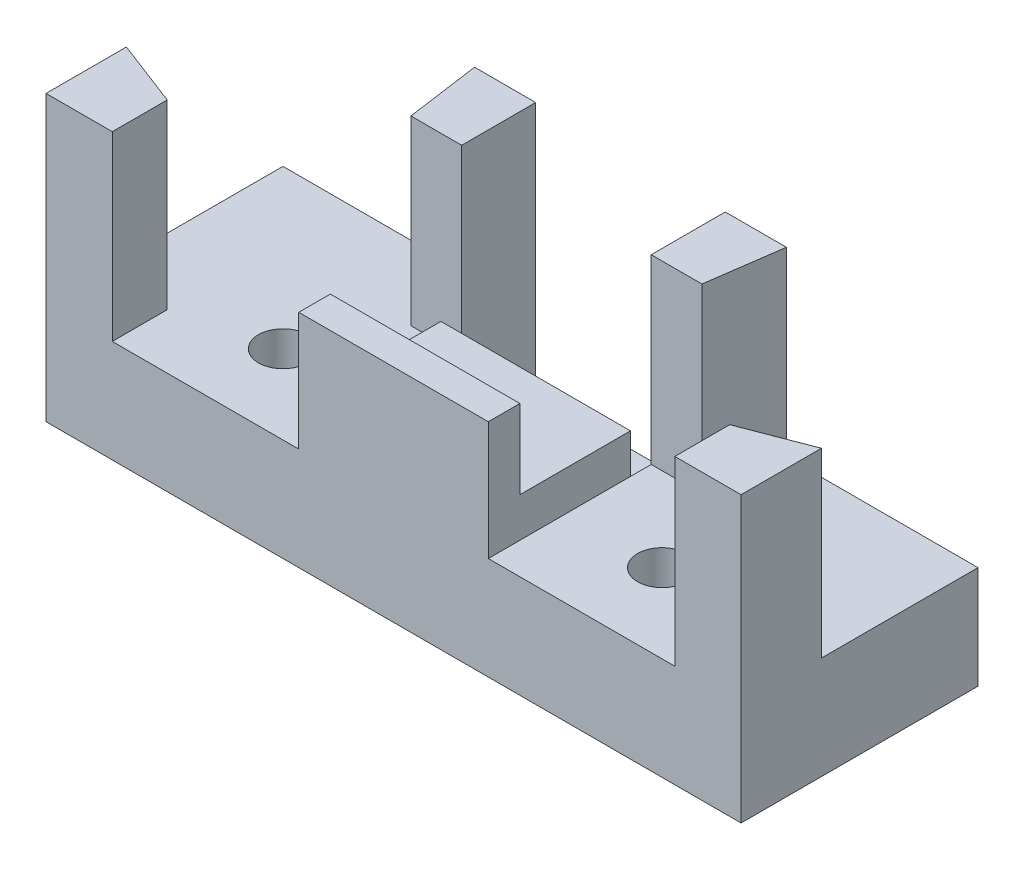
SolidWorks part; units mm, degrees
ref_plane "Front Plane" through (0, 0, 0) normal (0, 0, 1) x (1, 0, 0)
ref_plane "Top Plane" through (0, 0, 0) normal (0, 1, 0) x (1, 0, 0)
ref_plane "Right Plane" through (0, 0, 0) normal (1, 0, 0) x (0, 0, -1)
sketch "Sketch1" plane through (0, 0, 0) normal (0, 1, 0) x (1, 0, 0)
  line L1 (0, 0) -> (44, 0)
  line L2 (0, 0) -> (0, -15)
  line L3 (0, -15) -> (44, -15)
  line L4 (44, 0) -> (44, -15)
  dimension "D1" = 15
  dimension "D2" = 44
extrude "Boss-Extrude1" add sketch "Sketch1" along normal blind 5
sketch "Sketch2" plane through (0, 5, 0) normal (0, 1, 0) x (1, 0, 0)
  line L0 (44, 0) -> (0, 0) construction
  line L1 (16, 0) -> (28, 0)
  line L2 (16, 0) -> (16, -15)
  line L3 (16, -15) -> (28, -15)
  line L4 (28, 0) -> (28, -15)
  line L5 (0, -15) -> (44, -15) construction
  line L6 (22, 0) -> (22, -15) construction
  dimension "D1" = 6
  dimension "D2" = 6
extrude "Boss-Extrude2" add sketch "Sketch2" along normal blind 4
sketch "Sketch3" plane through (0, 5, 0) normal (0, 1, 0) x (1, 0, 0)
  line L0 (28, -15) -> (44, -15) construction
  line L4 (0, -15) -> (16, -15) construction
  line L5 (28, -15) -> (28, 0) construction
  line L6 (16, 0) -> (16, -15) construction
  circle A0 centre (10, -10) radius 1.55
  circle A1 centre (34, -10) radius 1.55
  dimension "D1" = 3.1
  dimension "D3" = 3.1
  dimension "D2" = 5
  dimension "D4" = 5
  dimension "D5" = 6
  dimension "D6" = 6
extrude "Cut-Extrude1" cut sketch "Sketch3" against normal blind 3
sketch "Sketch4" plane through (0, 9, 0) normal (0, 1, 0) x (1, 0, 0)
  line L1 (16, -15) -> (28, -15) construction
  line L2 (16, 0) -> (16, -15) construction
  circle A0 centre (22, -10) radius 1.55
  dimension "D1" = 3.1
  dimension "D2" = 5
  dimension "D3" = 6
extrude "Cut-Extrude2" cut sketch "Sketch4" against normal blind 3
sketch "Sketch6" plane through (0, 9, 0) normal (0, 1, 0) x (1, 0, 0)
  line L0 (16, 0) -> (16, -15) construction
  line L1 (16, -13) -> (28, -13)
  line L2 (16, -13) -> (16, -15)
  line L3 (16, -15) -> (28, -15)
  line L4 (28, -13) -> (28, -15)
  dimension "D1" = 2
extrude "Boss-Extrude4" add sketch "Sketch6" along normal blind 5
sketch "Sketch8" plane through (0, 5, 0) normal (0, 1, 0) x (1, 0, 0)
  line L0 (34, -10) -> (44, -10) construction
  line L1 (44, -15) -> (44, 0) construction
  line L2 (34, -10) -> (44, -6.1614) construction
  line L3 (34, -10) -> (35.4054, 0) construction
  line L4 (44, 0) -> (28, 0) construction
  line L5 (34.7027, -5) -> (31.2368, -4.5129) construction
  line L6 (31.2368, -4.5129) -> (29.8332, -14.4994) construction
  line L7 (34, -10) -> (31.2123, -4.6869) construction
  line L8 (31.2123, -4.6869) -> (31.871, 0)
  line L11 (39, -8.0807) -> (40.2543, -11.3482) construction
  line L12 (40.2543, -11.3482) -> (30.7411, -15) construction
  line L13 (28, -15) -> (44, -15) construction
  line L14 (34, -10) -> (39.804, -11.5211) construction
  line L15 (39.804, -11.5211) -> (44, -9.9104)
  line L16 (22, 0) -> (22, -15) construction
  line L17 (28, 0) -> (16, 0) construction
  line L18 (16, -15) -> (28, -15) construction
  line L20 (28, 0) -> (31.871, 0)
  line L22 (44, -15) -> (44, -9.9104)
  line L24 (12.7877, -4.6869) -> (12.129, 0)
  line L25 (16, 0) -> (12.129, 0)
  line L27 (4.196, -11.5211) -> (0, -9.9104)
  line L28 (0, -15) -> (0, -9.9104)
  line L29 (31.2123, -4.6869) -> (28, -4.6869)
  line L30 (28, -13) -> (28, 0) construction
  line L31 (28, -4.6869) -> (28, 0)
  line L32 (39.804, -11.5211) -> (39.804, -15)
  line L33 (39.804, -15) -> (44, -15)
  line L34 (12.7877, -4.6869) -> (16, -4.6869)
  line L35 (16, -4.6869) -> (16, 0)
  line L36 (4.196, -11.5211) -> (4.196, -15)
  line L37 (4.196, -15) -> (0, -15)
  dimension "D1" = 21
  dimension "D2" = 82
  dimension "D3" = 3.5
  dimension "D4" = 90
  dimension "D5" = 6
  dimension "D6" = 90
  dimension "D7" = 3.5
  dimension "D8" = 6
  dimension "D9" = 90
extrude "Boss-Extrude5" add sketch "Sketch8" along normal blind 13
sketch "Sketch10" plane through (0, 9, 0) normal (0, 1, 0) x (1, 0, 0)
  line L0 (28, -13) -> (28, -4.6869) construction
  line L1 (16, 0) -> (28, 0)
  line L2 (16, 0) -> (16, -6)
  line L3 (16, -6) -> (28, -6)
  line L4 (28, 0) -> (28, -6)
  dimension "D1" = 6
extrude "Cut-Extrude4" cut sketch "Sketch10" against normal blind 7
sketch "Sketch11" plane through (0, 5, 0) normal (0, 1, 0) x (1, 0, 0)
  line L0 (16, -15) -> (16, -4.6869)
  line L1 (16, -4.6869) -> (12.7877, -4.6869)
  line L2 (12.7877, -4.6869) -> (12.129, 0)
  line L3 (12.129, 0) -> (0, 0)
  line L4 (0, 0) -> (0, -9.9104)
  line L5 (0, -9.9104) -> (4.196, -11.5211)
  line L6 (4.196, -11.5211) -> (4.196, -15)
  line L7 (4.196, -15) -> (16, -15)
  line L8 (22, 0) -> (22, -15) construction
  line L9 (28, 0) -> (16, 0) construction
  line L10 (16, -15) -> (28, -15) construction
  line L11 (39.804, -11.5211) -> (39.804, -15)
  line L12 (44, -9.9104) -> (39.804, -11.5211)
  line L13 (44, 0) -> (44, -9.9104)
  line L14 (31.871, 0) -> (44, 0)
  line L15 (31.2123, -4.6869) -> (31.871, 0)
  line L16 (28, -4.6869) -> (31.2123, -4.6869)
  line L17 (28, -15) -> (28, -4.6869)
  line L18 (39.804, -15) -> (28, -15)
  circle A0 centre (10, -10) radius 1.55
  circle A1 centre (34, -10) radius 1.55
extrude "Boss-Extrude6" add sketch "Sketch11" along normal blind 1.5
